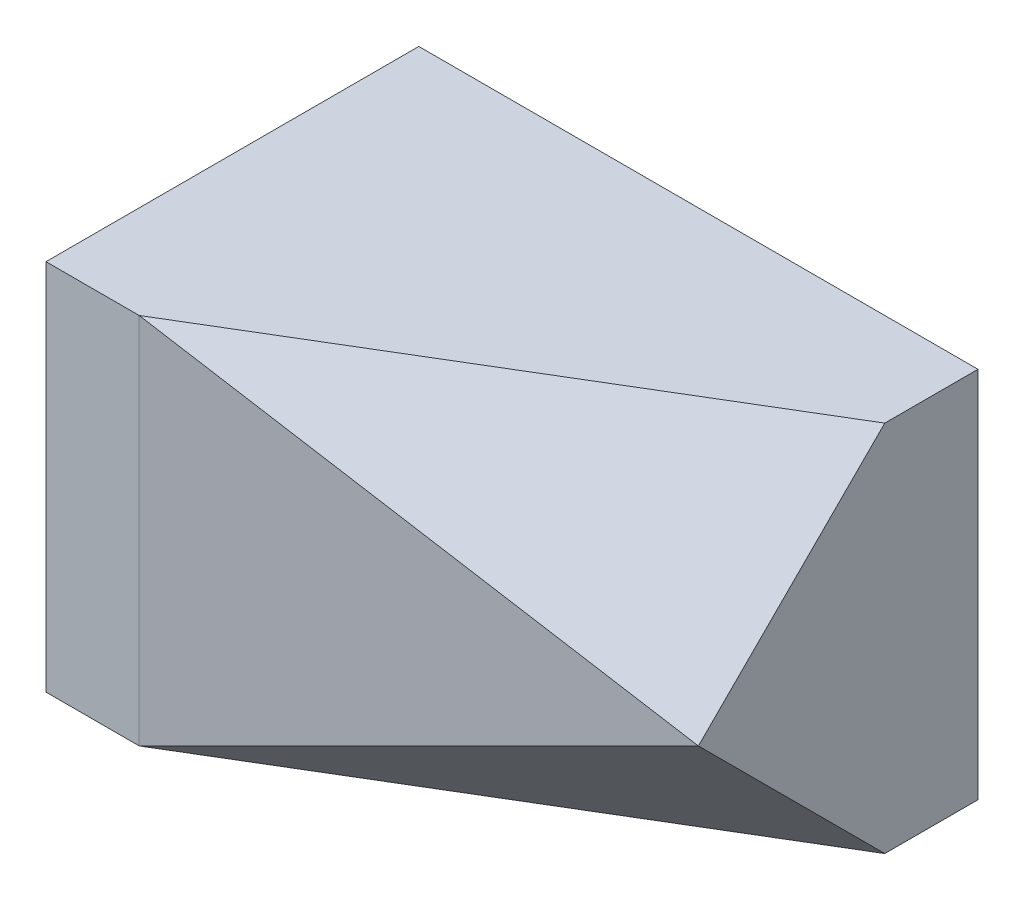
SolidWorks part; units mm, degrees
ref_plane "Front Plane" through (0, 0, 0) normal (0, 0, 1) x (1, 0, 0)
ref_plane "Top Plane" through (0, 0, 0) normal (0, 1, 0) x (1, 0, 0)
ref_plane "Right Plane" through (0, 0, 0) normal (1, 0, 0) x (0, 0, -1)
sketch "Sketch1" plane through (0, 0, 0) normal (0, 0, 1) x (1, 0, 0)
  line L0 (0, 0) -> (0, 1016)
  line L1 (0, 1016) -> (1524, 1016)
  line L2 (1524, 1016) -> (1524, 0)
  line L3 (1524, 0) -> (0, 0)
  line L4 (254, 1016) -> (254, 0)
  dimension "D1" = 1016
  dimension "D2" = 1524
  dimension "D3" = 1270
extrude "Boss-Extrude1" add sketch "Sketch1" along normal blind 1016 contours L1 L4 L3 L2 | L4 L1 L0 L3
sketch "Sketch3" plane through (0, 0, 1016) normal (0, 0, 1) x (1, 0, 0)
  line L0 (254, 0) -> (254, 1016)
  line L1 (1524, 0) -> (0, 0) construction
  line L2 (0, 1016) -> (1524, 1016) construction
  line L4 (1524, 1016) -> (1524, 0) construction
  dimension "D1" = 1270
sketch "Sketch4" plane through (1524, 0, 0) normal (1, 0, 0) x (0, 0, -1)
  line L0 (-254, 1016) -> (-762, 508)
  line L1 (-1016, 1016) -> (0, 1016) construction
  line L2 (-762, 508) -> (-254, 0)
  line L3 (-1016, 0) -> (0, 0) construction
  line L4 (-1016, 508) -> (0, 508) construction
  line L5 (-1016, 1016) -> (-1016, 0) construction
  line L6 (0, 1016) -> (0, 0) construction
  line L7 (-762, 508) -> (-1016, 254)
  line L8 (-762, 508) -> (-1016, 762)
  dimension "D1" = 254
  dimension "D2" = 254
  dimension "D3" = 508
ref_plane "Plane2" through (555.3559, 925.5932, 925.5932) normal (-0.3906, -0.6509, -0.6509) x (-0.9206, 0.2762, 0.2762)
other "SurfaceCut2"
ref_plane "Plane3" through (297.0508, -495.0847, 495.0847) normal (-0.3906, 0.6509, -0.6509) x (-0.9206, -0.2762, 0.2762)
other "SurfaceCut3"
ref_plane "Plane4" through (205.1538, 0, 1025.7692) normal (-0.1961, 0, -0.9806) x (-0.9806, 0, 0.1961)
other "SurfaceCut4"
